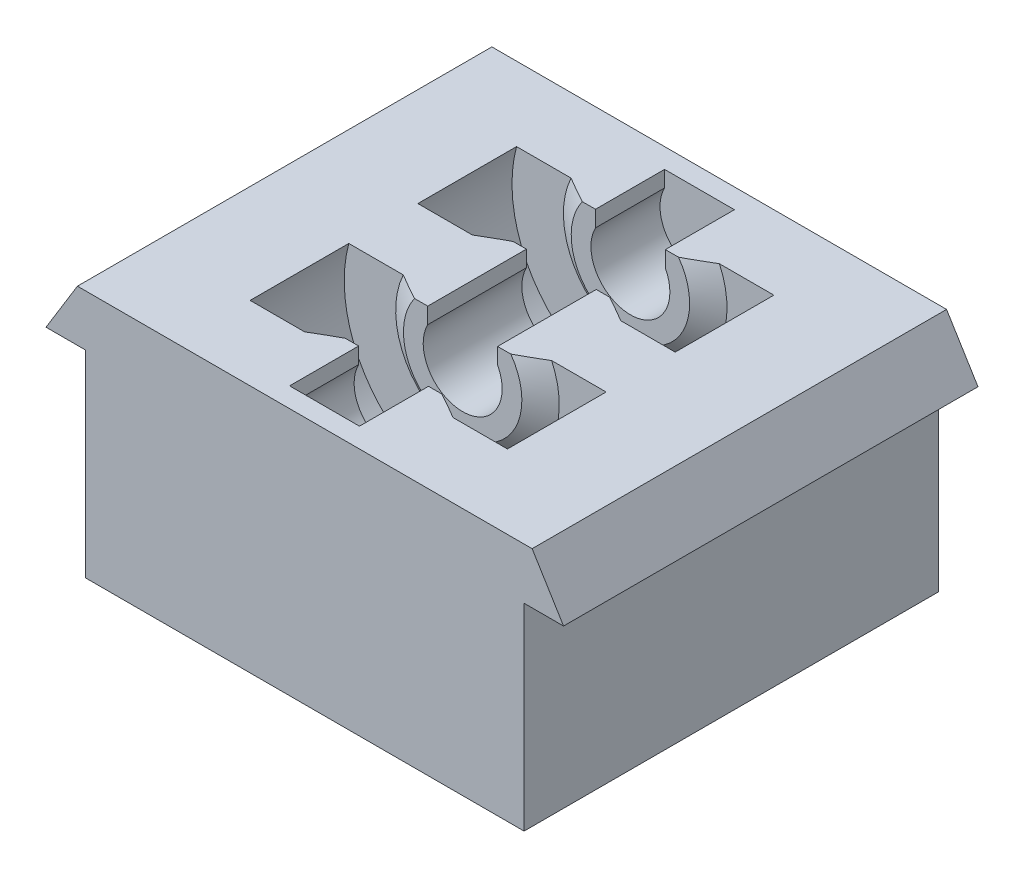
SolidWorks part; units mm, degrees
material "Nylon 101"
ref_plane "Front Plane" through (0, 0, 0) normal (0, 0, 1) x (1, 0, 0)
ref_plane "Top Plane" through (0, 0, 0) normal (0, 1, 0) x (1, 0, 0)
ref_plane "Right Plane" through (0, 0, 0) normal (1, 0, 0) x (0, 0, -1)
sketch "Sketch1" plane through (0, 0, 0) normal (0, 0, 1) x (1, 0, 0)
  line L0 (0, 38.5729) -> (0, -39.8293) construction
  line L1 (-23.0394, 7.5774) -> (-13.0394, 7.5774)
  line L2 (23.0394, 7.5774) -> (26.225, 2.3812)
  line L3 (26.225, 2.3812) -> (22.225, 2.3812)
  line L4 (22.225, 2.3812) -> (22.225, -17.6187)
  line L5 (22.225, -17.6187) -> (-22.225, -17.6188)
  line L6 (0, 15.0813) -> (38.1959, 15.0812) construction
  line L7 (-22.225, 2.3812) -> (-22.225, -17.6188)
  line L8 (-26.225, 2.3812) -> (-22.225, 2.3812)
  line L9 (-23.0394, 7.5774) -> (-26.225, 2.3812)
  line L10 (13.0394, 7.5774) -> (23.0394, 7.5774)
  arc A0 (13.0394, 7.5774) -> (-13.0394, 7.5774) centre (0, 0) ccw construction
  circle A1 centre (0, 4.0813) radius 11 construction
  arc A2 (-13.0394, 7.5774) -> (13.0394, 7.5774) centre (0, 4.0813) ccw
  point P14 (0, -17.6187)
  point P17 (0, 7.407)
  dimension "D1" = 20
  dimension "D3" = 30.1625
  dimension "D5" = 22
  dimension "D8" = 13.5
  dimension "D2" = 12.7
  dimension "D4" = 22.225
  dimension "D6" = 10
  dimension "D7" = 4
extrude "Boss-Extrude1" add sketch "Sketch1" along normal mid plane 25
ref_plane "Plane1" through (0, 0, 5) normal (0, 0, 1) x (1, 0, 0)
sketch "Sketch2" plane through (0, 0, 5) normal (0, 0, 1) x (1, 0, 0)
  line L0 (-3.5394, 5.9447) -> (-3.5394, 7.5774)
  line L1 (-3.5394, 7.5774) -> (-13.0394, 7.5774)
  line L2 (0, 4.0813) -> (0, 18.6961) construction
  line L3 (3.5394, 5.9447) -> (3.5394, 7.5774)
  line L4 (3.5394, 7.5774) -> (13.0394, 7.5774)
  arc A0 (-3.5394, 5.9447) -> (3.5394, 5.9447) centre (0, 4.0813) ccw
  arc A1 (-13.0394, 7.5774) -> (13.0394, 7.5774) centre (0, 4.0813) ccw construction
  circle A2 centre (0, 4.0813) radius 11 construction
  arc A3 (-13.0394, 7.5774) -> (13.0394, 7.5774) centre (0, 4.0813) ccw
  dimension "D1" = 22
  dimension "D2" = 4
  dimension "D3" = 9.5
extrude "Boss-Extrude2" add sketch "Sketch2" along normal up to surface (7.5 mm away) up to face at (0, -1.2399, 12.5)
ref_plane "Plane2" through (0, 0, -5) normal (0, 0, 1) x (1, 0, 0)
sketch "Sketch3" plane through (0, 0, -5) normal (0, 0, 1) x (1, 0, 0)
  line L4 (3.5394, 7.5774) -> (3.5394, 5.9447)
  line L5 (13.0394, 7.5774) -> (3.5394, 7.5774)
  line L6 (-3.5394, 7.5774) -> (-13.0394, 7.5774)
  line L7 (-3.5394, 5.9447) -> (-3.5394, 7.5774)
  line L8 (3.5394, 7.5774) -> (3.5394, 5.9447)
  line L9 (13.0394, 7.5774) -> (3.5394, 7.5774)
  line L10 (-3.5394, 7.5774) -> (-13.0394, 7.5774)
  line L11 (-3.5394, 5.9447) -> (-3.5394, 7.5774)
  arc A2 (-3.5394, 5.9447) -> (3.5394, 5.9447) centre (0, 4.0813) ccw
  arc A3 (-13.0394, 7.5774) -> (13.0394, 7.5774) centre (0, 4.0813) ccw
  arc A4 (-3.5394, 5.9447) -> (3.5394, 5.9447) centre (0, 4.0813) ccw
  arc A5 (-13.0394, 7.5774) -> (13.0394, 7.5774) centre (0, 4.0813) ccw
  dimension "D1" = 0
extrude "Boss-Extrude3" add sketch "Sketch3" against normal up to surface (7.5 mm away) up to face at (0, -1.2399, -12.5)
ref_plane "Plane3" through (0, 4.0813, 0) normal (0, 1, 0) x (1, 0, 0)
sketch "Sketch4" plane through (0, 4.0813, 0) normal (0, 1, 0) x (1, 0, 0)
  line L0 (-4, -5) -> (-4, -3.5)
  line L1 (-4, -3.5) -> (-6, -3.5)
  line L2 (-6, -3.5) -> (-8.2894, -5)
  line L3 (-3.5394, -5) -> (-13.0394, -5) construction
  line L4 (0, 0) -> (-40.6317, 0) construction
  line L5 (-4, 5) -> (-4, 3.5)
  line L6 (-4, 3.5) -> (-6, 3.5)
  line L7 (-6, 3.5) -> (-8.2894, 5)
  line L8 (-8.2894, 5) -> (-4, 5)
  line L9 (-8.2894, -5) -> (-4, -5)
  line L10 (0, 0) -> (0, 12.6772) construction
  dimension "D1" = 2
  dimension "D2" = 7
  dimension "D3" = 4
revolve "Revolve1" add sketch "Sketch4" angle 360 about L10
sketch "Sketch5" plane through (0, 7.5774, 0) normal (0, 1, 0) x (1, 0, 0)
  line L4 (22.225, 12.5) -> (-22.225, 12.5)
  line L5 (22.225, -12.5) -> (22.225, 12.5)
  line L6 (-22.225, -12.5) -> (22.225, -12.5)
  line L7 (-22.225, 12.5) -> (-22.225, -12.5)
  line L8 (22.225, 12.5) -> (-22.225, 12.5)
  line L9 (22.225, -12.5) -> (22.225, 12.5)
  line L10 (-22.225, -12.5) -> (22.225, -12.5)
  line L11 (-22.225, 12.5) -> (-22.225, -12.5)
  dimension "D1" = 0
extrude "Cut-Extrude1" cut sketch "Sketch5" along normal blind 10
sketch "Sketch6" plane through (0, 7.5774, 0) normal (0, 1, 0) x (1, 0, 0)
  line L0 (-3.5394, 5) -> (-3.5394, -5)
  line L1 (-3.5394, -5) -> (3.5394, -5)
  line L2 (3.5394, -5) -> (3.5394, 5)
  line L3 (3.5394, 5) -> (-3.5394, 5)
extrude "Cut-Extrude2" cut sketch "Sketch6" against normal up to surface (3.4962 mm away)
sketch "Sketch7" plane through (0, 0, 12.5) normal (0, 0, 1) x (1, 0, 0)
  line L0 (-22.225, 2.3812) -> (-22.225, 7.5774)
  line L1 (-3.5394, 7.5774) -> (-23.0394, 7.5774) construction
  line L2 (-22.225, 7.5774) -> (22.225, 7.5774)
  line L3 (23.0394, 7.5774) -> (3.5394, 7.5774) construction
  line L4 (22.225, 7.5774) -> (22.225, 2.3812)
  line L5 (22.225, 2.3812) -> (22.225, -12.4226)
  line L6 (22.225, -17.6187) -> (22.225, 2.3812) construction
  line L7 (22.225, -12.4226) -> (-22.225, -12.4226)
  line L8 (-22.225, 2.3812) -> (-22.225, -17.6188) construction
  line L9 (-22.225, -12.4226) -> (-22.225, 2.3812)
  dimension "D1" = 20
extrude "Boss-Extrude4" add sketch "Sketch7" against normal blind 2
mirror "Mirror1" about plane through (0, 0, 0) normal (0, 0, 1) of "Boss-Extrude4"
ref_plane "Plane4" through (0, 0, -8.5) normal (0, 0, -1) x (-1, 0, 0)
other "SurfaceCut1"
mirror "Mirror2" about plane through (0, 0, -8.5) normal (0, 0, -1) of bodies 112
sketch "Sketch8" plane through (0, 7.5774, 0) normal (0, 1, 0) x (1, 0, 0)
  line L0 (-3.5394, 8.5) -> (3.5394, 8.5) construction
  line L1 (-3.5394, 13.5) -> (-3.5394, 3.5) construction
  line L2 (3.5394, 13.5) -> (3.5394, 3.5) construction
  circle A0 centre (0, 0) radius 1.5
  circle A1 centre (0, 17) radius 1.5
  dimension "D1" = 3
extrude "Cut-Extrude3" cut sketch "Sketch8" against normal blind 40
